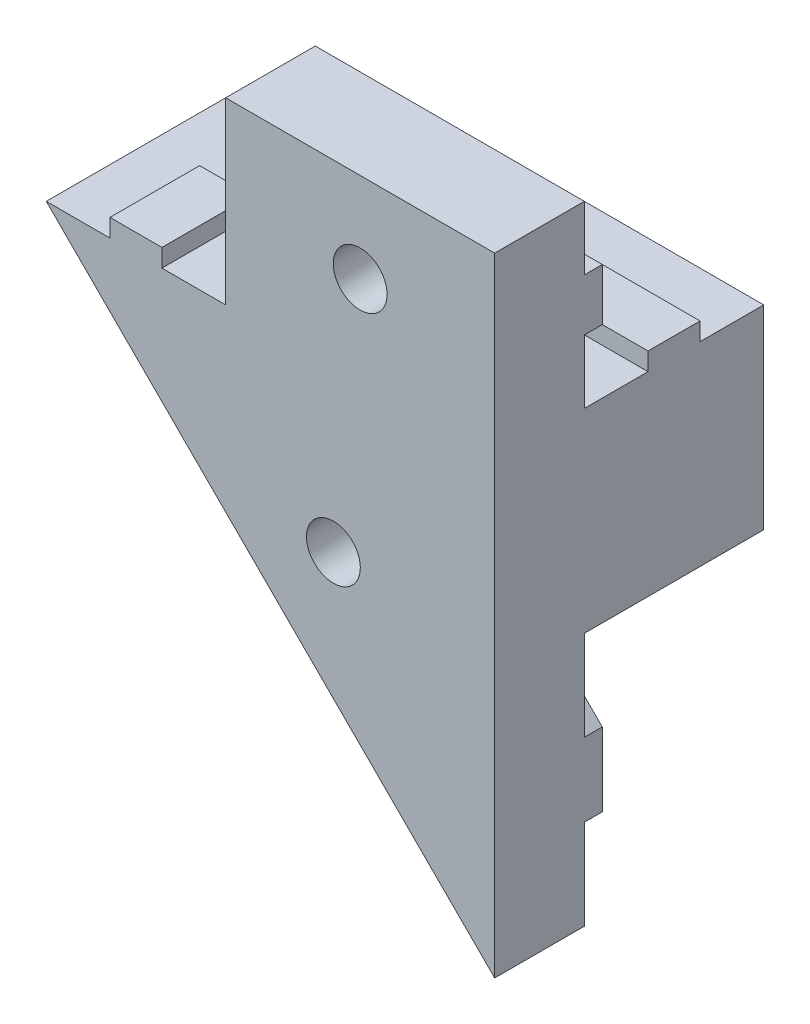
SolidWorks part; units mm, degrees
ref_plane "Front Plane" through (0, 0, 0) normal (0, 0, 1) x (1, 0, 0)
ref_plane "Top Plane" through (0, 0, 0) normal (0, 1, 0) x (1, 0, 0)
ref_plane "Right Plane" through (0, 0, 0) normal (1, 0, 0) x (0, 0, -1)
ref_plane "FrontPlane+10mm" through (0, 0, 10) normal (0, 0, 1) x (1, 0, 0)
sketch "Sketch1" plane through (0, 0, 0) normal (0, 0, 1) x (1, 0, 0)
  line L0 (-290, 0) -> (-10, 0) construction
  line L1 (0, 0) -> (-90, -90) construction
  line L2 (-10, 0) -> (0, 0) construction
  line L3 (-10, 0) -> (-10, 10) construction
  line L4 (-10, 10) -> (0, 10) construction
  line L5 (0, 0) -> (0, 10) construction
  line L6 (-90, -90) -> (-210, -90) construction
  line L7 (-300, 10) -> (-290, 10) construction
  line L8 (-300, 10) -> (-300, 0) construction
  line L9 (0, 0) -> (-10, 0)
  line L10 (-290, 10) -> (-290, 0) construction
  line L11 (-210, -90) -> (-300, 0) construction
  line L12 (-88.1335, -73.9914) -> (-16.0086, -1.8665) construction
  line L13 (-100, -80) -> (-90, -80) construction
  line L14 (-100, -80) -> (-100, -90) construction
  line L15 (-10, 0) -> (-10, 10)
  line L16 (-90, -80) -> (-90, -90) construction
  line L17 (-16.0086, -1.8665) -> (-8.9376, -8.9376) construction
  line L18 (-88.1335, -73.9914) -> (-81.0624, -81.0624) construction
  line L19 (-16.0086, -1.8665) -> (0, 0) construction
  line L20 (-88.1335, -73.9914) -> (-90, -90) construction
  line L21 (-10, 10) -> (-25, 10)
  line L22 (0, 0) -> (-8.9376, -8.9376)
  line L23 (-8.9376, -8.9376) -> (-16.0086, -1.8665)
  line L24 (-16.0086, -1.8665) -> (-25, -10.8579)
  line L25 (-25, -10.8579) -> (-25, 10)
  dimension "D1" = 10
  dimension "D2" = 10
  dimension "D3" = 300
  dimension "D4" = 10
  dimension "D5" = 120
  dimension "D6" = 135
  dimension "D7" = 45
  dimension "D8" = 45
  dimension "D9" = 127.2792
  dimension "D10" = 10
  dimension "D11" = 10
  dimension "D12" = 10
  dimension "D13" = 102
  dimension "D14" = 25
extrude "Main" add sketch "Sketch1" along normal blind 15
sketch "Sketch4" plane through (0, 0, 0) normal (0, 0, -1) x (-1, 0, 0)
  line L1 (10, 0) -> (25, 0)
  line L2 (10, 0) -> (10, 10)
  line L3 (10, 10) -> (25, 10)
  line L4 (25, 0) -> (25, 10)
extrude "Cut-Extrude2" cut sketch "Sketch4" against normal blind 10
sketch "Sketch2" plane through (0, 0, 10) normal (0, 0, -1) x (-1, 0, 0)
  line L0 (10, 0) -> (10, 10) construction
  line L1 (10, 6.45) -> (25, 6.45)
  line L2 (10, 6.45) -> (10, 3.55)
  line L3 (10, 3.55) -> (25, 3.55)
  line L4 (25, 6.45) -> (25, 3.55)
  line L5 (25, 0) -> (25, -10.8579) construction
  line L6 (10, 10) -> (25, 10) construction
  dimension "D1" = 3.55
  dimension "D2" = 2.9
extrude "Boss-Extrude3" add sketch "Sketch2" along normal blind 1
sketch "Sketch5" plane through (-7.0711, 7.0711, 0) normal (0.7071, -0.7071, 0) x (0, 0, -1)
  line L0 (-15, -25.3553) -> (0, -25.3553) construction
  line L1 (-3.55, -25.3553) -> (-6.45, -25.3553)
  line L2 (-3.55, -25.3553) -> (-3.55, -12.6396)
  line L3 (-3.55, -12.6396) -> (-6.45, -12.6396)
  line L4 (-6.45, -25.3553) -> (-6.45, -12.6396)
  line L5 (-15, -12.6396) -> (0, -12.6396) construction
  line L6 (0, -25.3553) -> (0, -12.6396) construction
  dimension "D1" = 3.55
  dimension "D2" = 2.9
extrude "Boss-Extrude4" add sketch "Sketch5" along normal blind 1
sketch "Sketch6" plane through (0, 0, 10) normal (0, 0, 1) x (1, 0, 0)
  line L0 (-25, -10.8579) -> (-16.0086, -1.8665)
  line L1 (-16.0086, -1.8665) -> (-8.9376, -8.9376)
  line L2 (-8.9376, -8.9376) -> (-25, -25)
  line L3 (-25, -10.8579) -> (-25, -25)
  line L4 (-12.4731, -5.402) -> (-19.5442, -12.4731) construction
  circle A0 centre (-16.0086, -8.9376) radius 1.5
  point P13 (-16.0086, -8.9376)
  dimension "D1" = 3
  dimension "D2" = 22.7157
  dimension "D3" = 14.1421
  dimension "D4" = 5
extrude "Boss-Extrude5" add sketch "Sketch6" along normal blind 5
sketch "Sketch7" plane through (0, 0, 10) normal (0, 0, -1) x (-1, 0, 0)
  line L0 (13.4984, -4.3767) -> (25, -15.8783)
  line L1 (25, -10.8579) -> (25, -25) construction
  line L3 (25, -15.8783) -> (25, -19.9795)
  line L4 (25, -19.9795) -> (11.4478, -6.4273)
  line L5 (11.4478, -6.4273) -> (13.4984, -4.3767)
  line L7 (8.9376, -8.9376) -> (16.0086, -1.8665) construction
  line L8 (16.0086, -1.8665) -> (8.9376, -8.9376) construction
  line L10 (25, -25) -> (0, 0) construction
  point P8 (15.2239, -13.4218)
  dimension "D1" = 2.9
  dimension "D2" = 3.55
extrude "Boss-Extrude6" add sketch "Sketch7" along normal blind 1
sketch "Sketch8" plane through (0, 0, 0) normal (0, 1, 0) x (1, 0, 0)
  line L0 (0, -15) -> (-10, -15) construction
  line L1 (-3.55, -15) -> (-6.45, -15)
  line L2 (-3.55, -15) -> (-3.55, -5)
  line L3 (-3.55, -5) -> (-6.45, -5)
  line L4 (-6.45, -15) -> (-6.45, -5)
  line L5 (0, -15) -> (0, 0) construction
  dimension "D1" = 3.55
  dimension "D2" = 2.9
  dimension "D3" = 10
extrude "Boss-Extrude7" add sketch "Sketch8" along normal blind 1
sketch "Sketch9" plane through (0, 0, 15) normal (0, 0, 1) x (1, 0, 0)
  line L0 (-10, 0) -> (-10, 10) construction
  line L1 (-10, 6.45) -> (-9, 6.45)
  line L2 (-10, 6.45) -> (-10, 3.55)
  line L3 (-10, 3.55) -> (-9, 3.55)
  line L4 (-9, 6.45) -> (-9, 3.55)
  line L5 (-10, 10) -> (-25, 10) construction
  dimension "D1" = 1
  dimension "D2" = 3.55
  dimension "D3" = 2.9
extrude "Boss-Extrude8" add sketch "Sketch9" against normal blind 10 separate body
sketch "Sketch11" plane through (0, 0, 0) normal (0, 1, 0) x (1, 0, 0)
  line L0 (0, -15) -> (0, 0) construction
  line L1 (0, 0) -> (-25, 0) construction
  circle A0 centre (-5, -5) radius 1.25
  dimension "D1" = 2.5
  dimension "D2" = 5
  dimension "D3" = 5
extrude "Cut-Extrude4" cut sketch "Sketch11" against normal through all
sketch "Sketch12" plane through (0, 0, 15) normal (0, 0, 1) x (1, 0, 0)
  circle A0 centre (-16.0086, -8.9376) radius 1.5
  arc A1 (-14.7117, -9.6913) -> (-16.7624, -7.6407) centre (-16.0086, -8.9376) ccw construction
extrude "Cut-Extrude5" cut sketch "Sketch12" against normal through all
sketch "Sketch13" plane through (0, 0, 0) normal (0, 1, 0) x (1, 0, 0)
  line L0 (-25, -10) -> (-25, 0) construction
  line L1 (-10, -3.55) -> (-25, -3.55)
  line L2 (-10, -3.55) -> (-10, -6.45)
  line L3 (-10, -6.45) -> (-25, -6.45)
  line L4 (-25, -3.55) -> (-25, -6.45)
  line L5 (0, -15) -> (0, 0) construction
  line L6 (0, 0) -> (-25, 0) construction
  dimension "D1" = 10
  dimension "D2" = 2.9
  dimension "D3" = 3.55
extrude "Boss-Extrude9" add sketch "Sketch13" along normal blind 1
sketch "Sketch15" plane through (0, 0, 10) normal (0, 0, -1) x (-1, 0, 0)
  line L1 (10, 10) -> (0, 10)
  line L2 (10, 10) -> (10, 0)
  line L3 (10, 0) -> (0, 0)
  line L4 (0, 10) -> (0, 0)
extrude "Cut-Extrude7" cut sketch "Sketch15" along normal through all
sketch "Sketch16" plane through (0, 0, 15) normal (0, 0, 1) x (1, 0, 0)
  line L0 (-10, 10) -> (-25, 10) construction
  line L3 (-25, 10) -> (-25, -25) construction
  circle A0 centre (-17.5, 5) radius 1.5
  dimension "D1" = 3
  dimension "D2" = 5
  dimension "D3" = 7.5
extrude "Cut-Extrude8" cut sketch "Sketch16" against normal through all
ref_plane "Plane1" through (-30, 0, 0) normal (-1, 0, 0) x (0, 0, 1)
mirror "Mirror1" about plane through (-30, 0, 0) normal (-1, 0, 0) of bodies 119 115
sketch "Sketch14" plane through (-25, 0, -10) normal (1, 0, 0) x (0, 0, -1)
  line L1 (-26.8666, 14.682) -> (3.9245, 14.682)
  line L2 (-26.8666, 14.682) -> (-26.8666, -28.2083)
  line L3 (-26.8666, -28.2083) -> (3.9245, -28.2083)
  line L4 (3.9245, 14.682) -> (3.9245, -28.2083)
extrude "Cut-Extrude6" cut sketch "Sketch14" along normal through all
